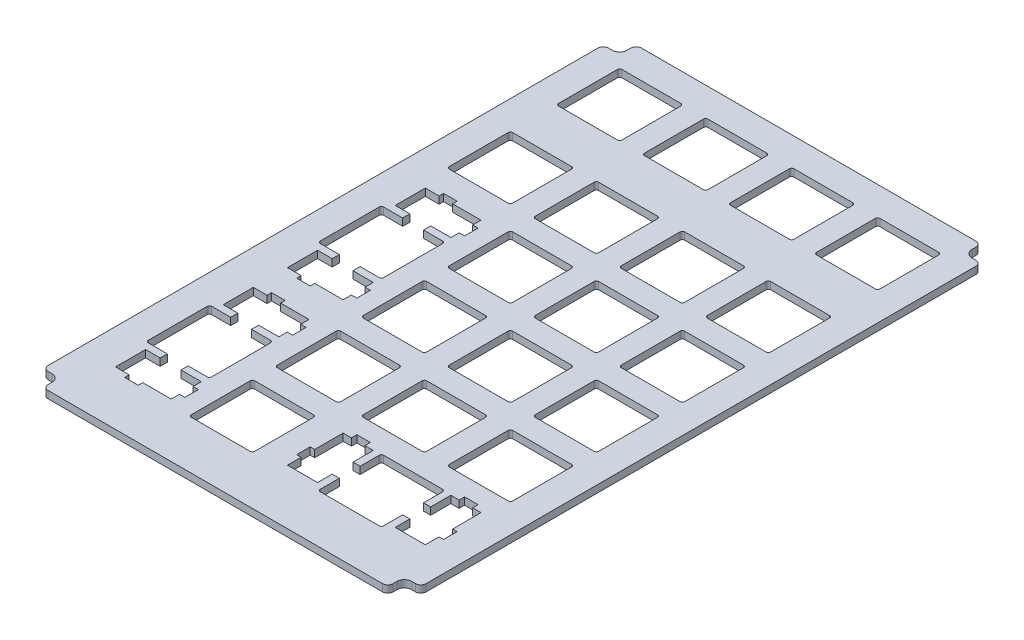
SolidWorks part; units mm, degrees
ref_plane "前视基准面" through (0, 0, 0) normal (0, 0, 1) x (1, 0, 0)
ref_plane "上视基准面" through (0, 0, 0) normal (0, 1, 0) x (1, 0, 0)
ref_plane "右视基准面" through (0, 0, 0) normal (1, 0, 0) x (0, 0, -1)
sketch "草图1" plane through (0, 0, 0) normal (0, 1, 0) x (1, 0, 0)
  line L17 (-11.3508, 119.1658) -> (-10.5008, 119.1658)
  line L18 (-8.8508, 120.8158) -> (-8.8508, 121.6658)
  line L19 (50.8492, 119.1658) -> (49.9992, 119.1658)
  line L20 (48.3492, 120.8158) -> (48.3492, 121.6658)
  line L21 (47.1992, 122.8158) -> (-7.7008, 122.8158)
  line L22 (-8.8508, 121.6658) -> (-8.8508, 120.8158)
  line L23 (-10.5008, 119.1658) -> (-11.3508, 119.1658)
  line L24 (-12.5008, 118.0158) -> (-12.5008, -3.4717)
  line L25 (-11.3508, -4.6217) -> (-10.5008, -4.6217)
  line L26 (-8.8508, -6.2717) -> (-8.8508, -7.1217)
  line L27 (-7.7008, -8.2717) -> (47.1992, -8.2717)
  line L28 (48.3492, -7.1217) -> (48.3492, -6.2717)
  line L29 (49.9992, -4.6217) -> (50.8492, -4.6217)
  line L30 (51.9992, -3.4717) -> (51.9992, 97.2055)
  line L37 (-11.3508, -4.6217) -> (-10.5008, -4.6217)
  line L38 (-8.8508, -6.2717) -> (-8.8508, -7.1217)
  line L43 (68.9992, 119.1658) -> (69.8492, 119.1658)
  line L44 (67.3492, 121.6658) -> (67.3492, 120.8158)
  line L45 (66.1992, 122.8158) -> (-7.7008, 122.8158)
  line L46 (70.9992, -3.4717) -> (70.9992, 118.0158)
  line L49 (66.1992, -8.2717) -> (-7.7008, -8.2717)
  line L50 (-12.5008, 118.0158) -> (-12.5008, -3.4717)
  line L53 (69.8492, -4.6217) -> (68.9992, -4.6217)
  line L54 (67.3492, -6.2717) -> (67.3492, -7.1217)
  line L266 (50.9992, 117.4055) -> (51.9992, 117.4055)
  line L268 (51.9992, 117.4055) -> (51.9992, 118.0158)
  line L270 (51.9992, 97.2055) -> (50.9992, 97.2055)
  line L272 (50.9992, 97.2055) -> (50.9992, 117.4055)
  arc A9 (-11.3508, 119.1658) -> (-12.5008, 118.0158) centre (-11.3508, 118.0158) ccw
  arc A10 (-10.5008, 119.1658) -> (-8.8508, 120.8158) centre (-10.5008, 120.8158) ccw
  arc A11 (-7.7008, 122.8158) -> (-8.8508, 121.6658) centre (-7.7008, 121.6658) ccw
  arc A12 (70.9992, 118.0158) -> (69.8492, 119.1658) centre (69.8492, 118.0158) ccw
  arc A13 (67.3492, 120.8158) -> (68.9992, 119.1658) centre (68.9992, 120.8158) ccw
  arc A14 (51.9992, 118.0158) -> (50.8492, 119.1658) centre (50.8492, 118.0158) ccw
  arc A15 (48.3492, 120.8158) -> (49.9992, 119.1658) centre (49.9992, 120.8158) ccw
  arc A16 (48.3492, 121.6658) -> (47.1992, 122.8158) centre (47.1992, 121.6658) ccw
  arc A17 (-7.7008, 122.8158) -> (-8.8508, 121.6658) centre (-7.7008, 121.6658) ccw
  arc A18 (-10.5008, 119.1658) -> (-8.8508, 120.8158) centre (-10.5008, 120.8158) ccw
  arc A19 (-11.3508, 119.1658) -> (-12.5008, 118.0158) centre (-11.3508, 118.0158) ccw
  arc A20 (-12.5008, -3.4717) -> (-11.3508, -4.6217) centre (-11.3508, -3.4717) ccw
  arc A21 (-8.8508, -6.2717) -> (-10.5008, -4.6217) centre (-10.5008, -6.2717) ccw
  arc A22 (-8.8508, -7.1217) -> (-7.7008, -8.2717) centre (-7.7008, -7.1217) ccw
  arc A23 (47.1992, -8.2717) -> (48.3492, -7.1217) centre (47.1992, -7.1217) ccw
  arc A24 (49.9992, -4.6217) -> (48.3492, -6.2717) centre (49.9992, -6.2717) ccw
  arc A25 (50.8492, -4.6217) -> (51.9992, -3.4717) centre (50.8492, -3.4717) ccw
  arc A32 (-12.5008, -3.4717) -> (-11.3508, -4.6217) centre (-11.3508, -3.4717) ccw
  arc A33 (-8.8508, -6.2717) -> (-10.5008, -4.6217) centre (-10.5008, -6.2717) ccw
  arc A34 (-8.8508, -7.1217) -> (-7.7008, -8.2717) centre (-7.7008, -7.1217) ccw
  arc A38 (67.3492, 121.6658) -> (66.1992, 122.8158) centre (66.1992, 121.6658) ccw
  arc A45 (69.8492, -4.6217) -> (70.9992, -3.4717) centre (69.8492, -3.4717) ccw
  arc A46 (68.9992, -4.6217) -> (67.3492, -6.2717) centre (68.9992, -6.2717) ccw
  arc A47 (66.1992, -8.2717) -> (67.3492, -7.1217) centre (66.1992, -7.1217) ccw
  dimension "D1" = 0
extrude "凸台-拉伸1" add sketch "草图1" along normal blind 1.6
sketch "草图6" plane through (0, 0, 0) normal (0, -1, 0) x (1, 0, 0)
  line L0 (-20.4509, -109.5658) -> (75.1048, -109.5658) construction
  line L1 (-30.8327, -47.4158) -> (78.7033, -47.4158) construction
  line L2 (29.2492, 25.694) -> (29.2492, -129.0357) construction
  line L3 (51.2492, -2.4158) -> (64.2492, -2.4158)
  line L4 (64.7492, -2.9158) -> (64.7492, -15.9158)
  line L5 (64.2492, -16.4158) -> (51.2492, -16.4158)
  line L6 (50.7492, -2.9158) -> (50.7492, -15.9158)
  line L7 (-28.6594, -9.4158) -> (85.6489, -9.4158) construction
  line L10 (67.2492, -99.3158) -> (-8.7508, -99.3158) construction
  line L11 (-9.5008, -100.0658) -> (-9.5008, -105.0658) construction
  line L12 (67.9992, -95.0158) -> (67.9992, 0.1842) construction
  line L13 (67.2492, 0.9342) -> (-8.7508, 0.9342) construction
  line L14 (67.9992, -105.0658) -> (67.9992, -100.0658) construction
  line L15 (67.9992, -119.0658) -> (67.9992, -114.0658) construction
  line L16 (-8.7508, -119.8158) -> (67.2492, -119.8158) construction
  line L17 (-9.5008, -114.0658) -> (-9.5008, -119.0658) construction
  line L18 (-9.5008, 0.1842) -> (-9.5008, -95.0158) construction
  line L19 (-8.7508, -95.7658) -> (67.2492, -95.7658) construction
  arc A0 (50.7492, -15.9158) -> (51.2492, -16.4158) centre (51.2492, -15.9158) ccw
  arc A1 (64.2492, -16.4158) -> (64.7492, -15.9158) centre (64.2492, -15.9158) ccw
  arc A2 (51.2492, -2.4158) -> (50.7492, -2.9158) centre (51.2492, -2.9158) ccw
  arc A3 (64.2492, -2.4158) -> (64.7492, -2.9158) centre (64.2492, -2.9158) cw
  dimension "D2" = 0.5
  dimension "D1" = 14
  dimension "D3" = 21.5
  dimension "D4" = 31
extrude "切除-拉伸3" cut sketch "草图6" against normal up to next (1.6 mm away)
pattern_linear "阵列(线性)1" count 5 spacing 19 along (0, 0, -1) count 4 spacing 19 along (-1, 0, 0) skipping (0, 3), (1, 3), (2, 3), (3, 3) of "切除-拉伸3"
pattern_linear "阵列(线性)2" count 2 spacing 100.15 along (0, 0, -1) count 4 spacing 19 along (-1, 0, 0) skipping (0, 1), (0, 2), (0, 3) of "切除-拉伸3"
sketch "草图3" plane through (0, 1.6, 0) normal (0, 1, 0) x (1, 0, 0)
  line L0 (-24.3873, 18.9158) -> (58.3219, 18.9158) construction
  line L1 (0.7492, -13.1729) -> (0.7492, 58.2769) construction
  line L2 (-6.2508, 12.4158) -> (-6.2508, 25.4158)
  line L3 (7.7492, 25.4158) -> (7.7492, 12.4158)
  line L4 (-5.7508, 25.9158) -> (-1.5508, 25.9158)
  line L9 (-6.2508, 25.9158) -> (7.7492, 11.9158) construction
  line L10 (-6.2508, 11.9158) -> (7.7492, 25.9158) construction
  line L11 (-1.5508, 25.9158) -> (-1.5508, 27.4958)
  line L12 (-4.7808, 27.4958) -> (-1.5508, 27.4958)
  line L13 (-4.7808, 27.4958) -> (-4.7808, 34.1458)
  line L14 (-4.7808, 34.1458) -> (-1.7508, 34.1458)
  line L15 (-1.7508, 34.1458) -> (-1.7508, 35.1458)
  line L16 (-1.7508, 35.1458) -> (1.2492, 35.1458)
  line L17 (1.2492, 35.1458) -> (1.2492, 34.1458)
  line L18 (1.2492, 34.1458) -> (7.5192, 34.1458)
  line L19 (7.5192, 34.1458) -> (7.5192, 32.3208)
  line L20 (7.5192, 32.3208) -> (8.7192, 32.3208)
  line L21 (8.7192, 32.3208) -> (8.7192, 29.3208)
  line L22 (8.7192, 29.3208) -> (7.5192, 29.3208)
  line L23 (7.5192, 29.3208) -> (7.5192, 27.4958)
  line L24 (7.5192, 27.4958) -> (3.0492, 27.4958)
  line L25 (3.0492, 27.4958) -> (3.0492, 25.9158)
  line L26 (3.0492, 25.9158) -> (7.2492, 25.9158)
  line L27 (3.0492, 11.9158) -> (7.2492, 11.9158)
  line L28 (3.0492, 10.3358) -> (3.0492, 11.9158)
  line L29 (7.5192, 10.3358) -> (3.0492, 10.3358)
  line L30 (7.5192, 8.5108) -> (7.5192, 10.3358)
  line L31 (8.7192, 8.5108) -> (7.5192, 8.5108)
  line L32 (8.7192, 5.5108) -> (8.7192, 8.5108)
  line L33 (7.5192, 5.5108) -> (8.7192, 5.5108)
  line L34 (7.5192, 3.6858) -> (7.5192, 5.5108)
  line L35 (1.2492, 3.6858) -> (7.5192, 3.6858)
  line L36 (1.2492, 2.6858) -> (1.2492, 3.6858)
  line L37 (-1.7508, 2.6858) -> (1.2492, 2.6858)
  line L38 (-1.7508, 3.6858) -> (-1.7508, 2.6858)
  line L39 (-4.7808, 3.6858) -> (-1.7508, 3.6858)
  line L40 (-4.7808, 10.3358) -> (-4.7808, 3.6858)
  line L41 (-4.7808, 10.3358) -> (-1.5508, 10.3358)
  line L42 (-1.5508, 11.9158) -> (-1.5508, 10.3358)
  line L43 (-5.7508, 11.9158) -> (-1.5508, 11.9158)
  line L46 (-6.2508, 50.4158) -> (-6.2508, 63.4158)
  line L47 (7.7492, 63.4158) -> (7.7492, 50.4158)
  line L48 (-5.7508, 63.9158) -> (-1.5508, 63.9158)
  line L49 (-1.5508, 63.9158) -> (-1.5508, 65.4958)
  line L50 (-4.7808, 65.4958) -> (-1.5508, 65.4958)
  line L51 (-4.7808, 65.4958) -> (-4.7808, 72.1458)
  line L52 (-4.7808, 72.1458) -> (-1.7508, 72.1458)
  line L53 (-1.7508, 72.1458) -> (-1.7508, 73.1458)
  line L54 (-1.7508, 73.1458) -> (1.2492, 73.1458)
  line L55 (1.2492, 73.1458) -> (1.2492, 72.1458)
  line L56 (1.2492, 72.1458) -> (7.5192, 72.1458)
  line L57 (7.5192, 72.1458) -> (7.5192, 70.3208)
  line L58 (7.5192, 70.3208) -> (8.7192, 70.3208)
  line L59 (8.7192, 70.3208) -> (8.7192, 67.3208)
  line L60 (8.7192, 67.3208) -> (7.5192, 67.3208)
  line L61 (7.5192, 67.3208) -> (7.5192, 65.4958)
  line L62 (7.5192, 65.4958) -> (3.0492, 65.4958)
  line L63 (3.0492, 65.4958) -> (3.0492, 63.9158)
  line L64 (3.0492, 63.9158) -> (7.2492, 63.9158)
  line L65 (3.0492, 49.9158) -> (7.2492, 49.9158)
  line L66 (3.0492, 48.3358) -> (3.0492, 49.9158)
  line L67 (7.5192, 48.3358) -> (3.0492, 48.3358)
  line L68 (7.5192, 46.5108) -> (7.5192, 48.3358)
  line L69 (8.7192, 46.5108) -> (7.5192, 46.5108)
  line L70 (8.7192, 43.5108) -> (8.7192, 46.5108)
  line L71 (7.5192, 43.5108) -> (8.7192, 43.5108)
  line L72 (7.5192, 41.6858) -> (7.5192, 43.5108)
  line L73 (1.2492, 41.6858) -> (7.5192, 41.6858)
  line L74 (1.2492, 40.6858) -> (1.2492, 41.6858)
  line L75 (-1.7508, 40.6858) -> (1.2492, 40.6858)
  line L76 (-1.7508, 41.6858) -> (-1.7508, 40.6858)
  line L77 (-4.7808, 41.6858) -> (-1.7508, 41.6858)
  line L78 (-4.7808, 48.3358) -> (-4.7808, 41.6858)
  line L79 (-4.7808, 48.3358) -> (-1.5508, 48.3358)
  line L80 (-1.5508, 49.9158) -> (-1.5508, 48.3358)
  line L81 (-5.7508, 49.9158) -> (-1.5508, 49.9158)
  line L82 (-6.2508, 63.9158) -> (7.7492, 49.9158) construction
  line L83 (-6.2508, 49.9158) -> (7.7492, 63.9158) construction
  line L84 (32.2492, 16.4158) -> (45.2492, 16.4158) construction
  arc A0 (-6.2508, 25.4158) -> (-5.7508, 25.9158) centre (-5.7508, 25.4158) cw
  arc A1 (7.2492, 25.9158) -> (7.7492, 25.4158) centre (7.2492, 25.4158) cw
  arc A2 (7.2492, 11.9158) -> (7.7492, 12.4158) centre (7.2492, 12.4158) ccw
  arc A3 (-6.2508, 12.4158) -> (-5.7508, 11.9158) centre (-5.7508, 12.4158) ccw
  arc A4 (-6.2508, 63.4158) -> (-5.7508, 63.9158) centre (-5.7508, 63.4158) cw
  arc A5 (7.2492, 63.9158) -> (7.7492, 63.4158) centre (7.2492, 63.4158) cw
  arc A6 (7.2492, 49.9158) -> (7.7492, 50.4158) centre (7.2492, 50.4158) ccw
  arc A7 (-6.2508, 50.4158) -> (-5.7508, 49.9158) centre (-5.7508, 50.4158) ccw
  point P4 (0.7492, 18.9158)
  point P5 (0.7492, 18.9158)
  point P17 (-3.6508, 25.9158)
  point P64 (0.7492, 56.9158)
  point P65 (0.7492, 56.9158)
  dimension "D1" = 14
  dimension "D2" = 4.2
  dimension "D3" = 1.58
  dimension "D4" = 3.23
  dimension "D5" = 6.65
  dimension "D6" = 3.03
  dimension "D7" = 3
  dimension "D8" = 1
  dimension "D9" = 6.27
  dimension "D10" = 3
  dimension "D11" = 1.2
  dimension "D12" = 0.5
  dimension "D13" = 13
  dimension "D14" = 45
  dimension "D15" = 4.47
  dimension "D16" = 2
  dimension "D17" = 2.5
  dimension "D18" = 38
extrude "切除-拉伸2" cut sketch "草图3" against normal up to surface (1.6 mm away) up to face at (57.7492, 0, -109.5658)
sketch "草图7" plane through (0, 1.6, 0) normal (0, 1, 0) x (1, 0, 0)
  line L1 (30.8591, 16.9848) -> (66.3802, 16.9848)
  line L2 (30.8591, 16.9848) -> (30.8591, 1.1193)
  line L3 (30.8591, 1.1193) -> (66.3802, 1.1193)
  line L4 (66.3802, 16.9848) -> (66.3802, 1.1193)
extrude "凸台-拉伸2" add sketch "草图7" against normal up to surface (1.6 mm away) up to face at (2.1472, 0, -18.9158)
sketch "草图8" plane through (0, 1.6, 0) normal (0, 1, 0) x (1, 0, 0)
  line L0 (26.7492, 9.4158) -> (76.4498, 9.4158) construction
  line L1 (26.7492, 15.9158) -> (26.7492, 2.9158) construction
  line L2 (48.2492, 23.7044) -> (48.2492, -8.9571) construction
  line L3 (48.2492, 2.4158) -> (48.2492, 16.4158) construction
  line L4 (48.2492, 9.4158) -> (41.7492, 9.4158) construction
  line L72 (58.6542, 16.1858) -> (56.8292, 16.1858)
  line L73 (58.6542, 17.3858) -> (58.6542, 16.1858)
  line L74 (61.6542, 17.3858) -> (58.6542, 17.3858)
  line L75 (61.6542, 16.1858) -> (61.6542, 17.3858)
  line L76 (63.4792, 16.1858) -> (61.6542, 16.1858)
  line L77 (63.4792, 9.9158) -> (63.4792, 16.1858)
  line L78 (64.4792, 9.9158) -> (63.4792, 9.9158)
  line L79 (64.4792, 6.9158) -> (64.4792, 9.9158)
  line L80 (63.4792, 6.9158) -> (64.4792, 6.9158)
  line L81 (63.4792, 3.8858) -> (63.4792, 6.9158)
  line L82 (56.8292, 3.8858) -> (63.4792, 3.8858)
  line L83 (56.8292, 7.1158) -> (56.8292, 3.8858)
  line L84 (55.2492, 7.1158) -> (56.8292, 7.1158)
  line L85 (55.2492, 2.9158) -> (55.2492, 7.1158)
  line L86 (41.7492, 2.4158) -> (54.7492, 2.4158)
  line L87 (41.2492, 7.1158) -> (41.2492, 2.9158)
  line L88 (39.6692, 7.1158) -> (41.2492, 7.1158)
  line L89 (39.6692, 3.8858) -> (39.6692, 7.1158)
  line L90 (33.0192, 3.8858) -> (39.6692, 3.8858)
  line L91 (33.0192, 6.9158) -> (33.0192, 3.8858)
  line L92 (32.0192, 6.9158) -> (33.0192, 6.9158)
  line L93 (32.0192, 9.9158) -> (32.0192, 6.9158)
  line L94 (33.0192, 9.9158) -> (32.0192, 9.9158)
  line L95 (33.0192, 16.1858) -> (33.0192, 9.9158)
  line L96 (34.8442, 16.1858) -> (33.0192, 16.1858)
  line L97 (34.8442, 17.3858) -> (34.8442, 16.1858)
  line L98 (37.8442, 17.3858) -> (34.8442, 17.3858)
  line L99 (37.8442, 16.1858) -> (37.8442, 17.3858)
  line L100 (39.6692, 16.1858) -> (37.8442, 16.1858)
  line L101 (39.6692, 11.7158) -> (39.6692, 16.1858)
  line L102 (41.2492, 11.7158) -> (39.6692, 11.7158)
  line L103 (41.2492, 15.9158) -> (41.2492, 11.7158)
  line L104 (54.7492, 16.4158) -> (41.7492, 16.4158)
  line L105 (55.2492, 11.7158) -> (55.2492, 15.9158)
  line L106 (56.8292, 11.7158) -> (55.2492, 11.7158)
  line L107 (56.8292, 16.1858) -> (56.8292, 11.7158)
  arc A8 (54.7492, 2.4158) -> (55.2492, 2.9158) centre (54.7492, 2.9158) ccw
  arc A9 (41.2492, 2.9158) -> (41.7492, 2.4158) centre (41.7492, 2.9158) ccw
  arc A10 (41.7492, 16.4158) -> (41.2492, 15.9158) centre (41.7492, 15.9158) ccw
  arc A11 (55.2492, 15.9158) -> (54.7492, 16.4158) centre (54.7492, 15.9158) ccw
  point P22 (48.2492, 9.4158)
extrude "切除-拉伸4" cut sketch "草图8" against normal up to surface (1.6 mm away) up to face at (2.1472, 0, -18.9158)
